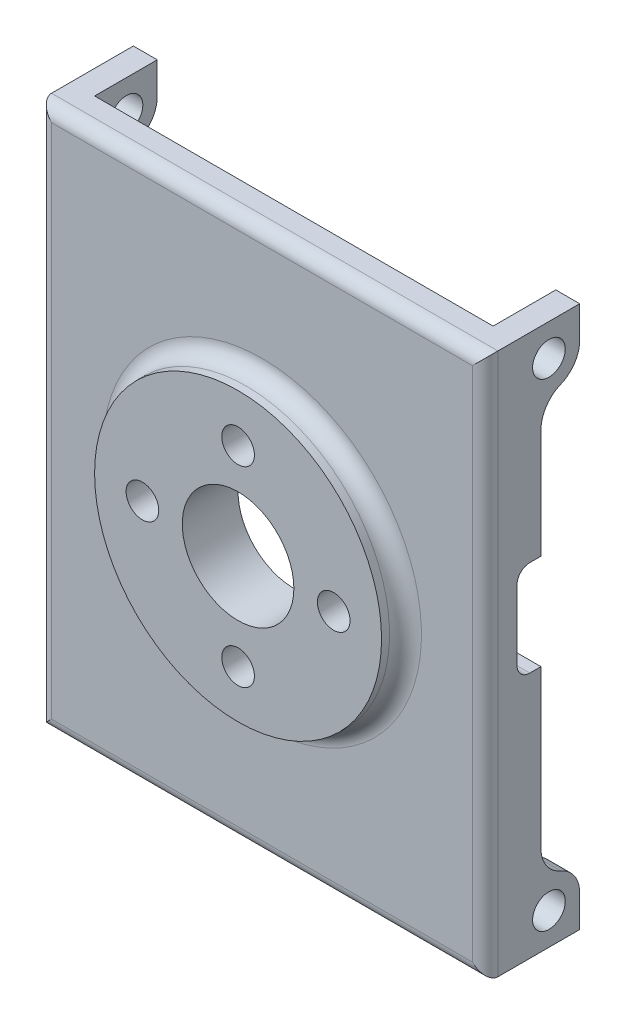
SolidWorks part; units mm, degrees
material "Tough 2000"
ref_plane "Front Plane" through (0, 0, 0) normal (0, 0, 1) x (1, 0, 0)
ref_plane "Top Plane" through (0, 0, 0) normal (0, 1, 0) x (1, 0, 0)
ref_plane "Right Plane" through (0, 0, 0) normal (1, 0, 0) x (0, 0, -1)
sketch "Sketch1" plane through (0, 0, 0) normal (0, 1, 0) x (1, 0, 0)
  line L0 (-14, 0) -> (14, 0)
  line L1 (14, 0) -> (14, 5.93)
  line L2 (14, 5.93) -> (12.5, 5.93)
  line L3 (12.5, 5.93) -> (12.5, 2)
  line L4 (12.5, 2) -> (-12.5, 2)
  line L5 (0, 2) -> (0, 0) construction
  line L6 (-12.5, 5.93) -> (-12.5, 2)
  line L7 (-14, 5.93) -> (-12.5, 5.93)
  line L8 (-14, 0) -> (-14, 5.93)
  dimension "D1" = 28
  dimension "D2" = 1.5
  dimension "D3" = 2
  dimension "D4" = 3.93
extrude "Boss-Extrude1" add sketch "Sketch1" along normal mid plane 34
sketch "Sketch2" plane through (-12.5, 0, 0) normal (1, 0, 0) x (0, 0, -1)
  line L0 (0, 0) -> (5.93, 0) construction
  line L1 (5.93, 17) -> (5.93, -17) construction
  line L2 (2, 17) -> (2, -17) construction
  circle A0 centre (4, 15) radius 1.025
  circle A1 centre (4, -15) radius 1.025
  dimension "D1" = 30
  dimension "D2" = 2
  dimension "D3" = 2.05
extrude "Cut-Extrude1" cut sketch "Sketch2" against normal mid plane 100
sketch "Sketch3" plane through (14, 0, 0) normal (1, 0, 0) x (0, 0, -1)
  line L0 (5.93, 17) -> (5.93, -17) construction
  line L1 (0, 0) -> (5.93, 0) construction
  line L2 (3.5, -13.1359) -> (3.5, 13.1359)
  line L3 (5.93, -15) -> (5.93, 15)
  line L4 (2, 17) -> (2, -17) construction
  arc A0 (3.5, 13.1359) -> (5.93, 15) centre (4, 15) ccw
  arc A1 (3.5, -13.1359) -> (5.93, -15) centre (4, -15) cw
  point P15 (3.5, 0)
  dimension "D1" = 1.5
extrude "Cut-Extrude2" cut sketch "Sketch3" against normal mid plane 100
fillet "Fillet1" radius 2 4 edges at (-13.25, 13.1359, -3.5) (13.25, -13.1359, -3.5) (-13.25, -13.1359, -3.5) (13.25, 13.1359, -3.5)
sketch "Sketch8" plane through (14, 0, 0) normal (1, 0, 0) x (0, 0, -1)
  line L0 (3.5, -11.3675) -> (3.5, 11.3675) construction
  line L1 (3.5, 4.5) -> (2, 4.5)
  line L2 (3.5, 4.5) -> (3.5, -1.5)
  line L3 (3.5, -1.5) -> (2, -1.5)
  line L4 (2, 4.5) -> (2, -1.5)
  point P6 (2, 1.5)
  dimension "D1" = 1.5
  dimension "D2" = 6
  dimension "D3" = 1.5
extrude "Cut-Extrude5" cut sketch "Sketch8" against normal blind 10
sketch "Sketch9" plane through (0, 0, 0) normal (0, 0, 1) x (1, 0, 0)
  circle A0 centre (0, 0) radius 9
  dimension "D1" = 18
extrude "Boss-Extrude2" add sketch "Sketch9" along normal blind 1.5
sketch "Sketch7" plane through (0, 0, -2) normal (0, 0, 1) x (1, 0, 0)
  circle A0 centre (0, 0) radius 3.5
  circle A5 centre (0, 0) radius 6 construction
  circle A6 centre (0, 6) radius 1.025
  circle A7 centre (0, -6) radius 1.025
  circle A8 centre (6, 0) radius 1.025
  circle A9 centre (-6, 0) radius 1.025
  dimension "D1" = 7
  dimension "D2" = 12
  dimension "D3" = 2.05
extrude "Cut-Extrude6" cut sketch "Sketch7" along normal blind 10
sketch "Sketch10" plane through (0, 0, -2) normal (0, 0, -1) x (-1, 0, 0)
  circle A0 centre (0, 6) radius 2
  circle A1 centre (-6, 0) radius 2
  circle A2 centre (0, -6) radius 2
  circle A3 centre (6, 0) radius 2
  dimension "D1" = 4
extrude "Cut-Extrude7" cut sketch "Sketch10" against normal blind 2
fillet "Fillet2" radius 1 1 edges at (9, 0, 0)
fillet "Fillet3" radius 0.8 4 edges at (-14, 0, 0) (0, 17, 0) (14, 0, 0) (0, -17, 0)
fillet "Fillet4" radius 0.8 2 edges at (13.25, 4.5, -2) (13.25, -1.5, -2)
